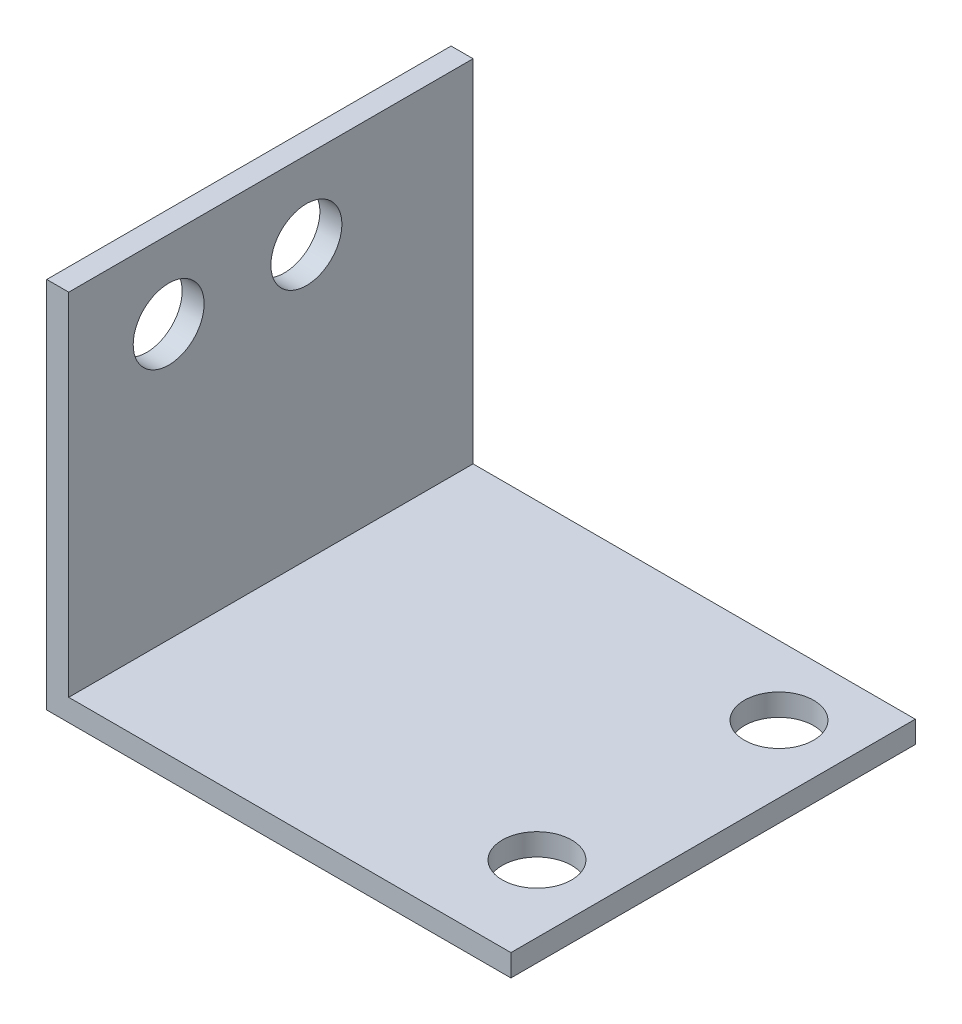
SolidWorks part; units mm, degrees
ref_plane "Front Plane" through (0, 0, 0) normal (0, 0, 1) x (1, 0, 0)
ref_plane "Top Plane" through (0, 0, 0) normal (0, 1, 0) x (1, 0, 0)
ref_plane "Right Plane" through (0, 0, 0) normal (1, 0, 0) x (0, 0, -1)
sketch "Sketch1" plane through (0, 0, 0) normal (0, 1, 0) x (1, 0, 0)
  line L0 (14.99, 12.1) -> (14.99, -9.9) construction
  line L1 (-21.1, 18.38) -> (21.1, 18.38)
  line L2 (-21.1, 18.38) -> (-21.1, -18.38)
  line L3 (-21.1, -18.38) -> (21.1, -18.38)
  line L4 (21.1, 18.38) -> (21.1, -18.38)
  line L5 (-21.1, 18.38) -> (21.1, -18.38) construction
  line L6 (-21.1, -18.38) -> (21.1, 18.38) construction
  circle A0 centre (14.99, 12.1) radius 3.15
  circle A1 centre (14.99, -9.9) radius 3.15
  point P0 (0, 0)
  dimension "D3" = 6.3
  dimension "D4" = 6.3
  dimension "D1" = 42.2
  dimension "D2" = 36.76
  dimension "D5" = 8.48
  dimension "D6" = 6.28
  dimension "D7" = 6.11
extrude "Base" add sketch "Sketch1" along normal blind 2
sketch "Sketch3" plane through (-21.1, 0, 0) normal (-1, 0, 0) x (0, 0, 1)
  line L1 (-18.38, 0) -> (18.38, 0)
  line L2 (-18.38, 0) -> (-18.38, 33.9)
  line L3 (-18.38, 33.9) -> (18.38, 33.9)
  line L4 (18.38, 0) -> (18.38, 33.9)
  line L5 (-3.225, 26.835) -> (9.295, 26.835) construction
  circle A0 centre (-3.225, 26.835) radius 3.225
  circle A1 centre (9.295, 26.835) radius 3.225
  dimension "D2" = 6.45
  dimension "D3" = 6.45
  dimension "D1" = 33.9
  dimension "D4" = 7.065
  dimension "D5" = 9.085
  dimension "D6" = 15.155
extrude "Tab" add sketch "Sketch3" against normal blind 2
